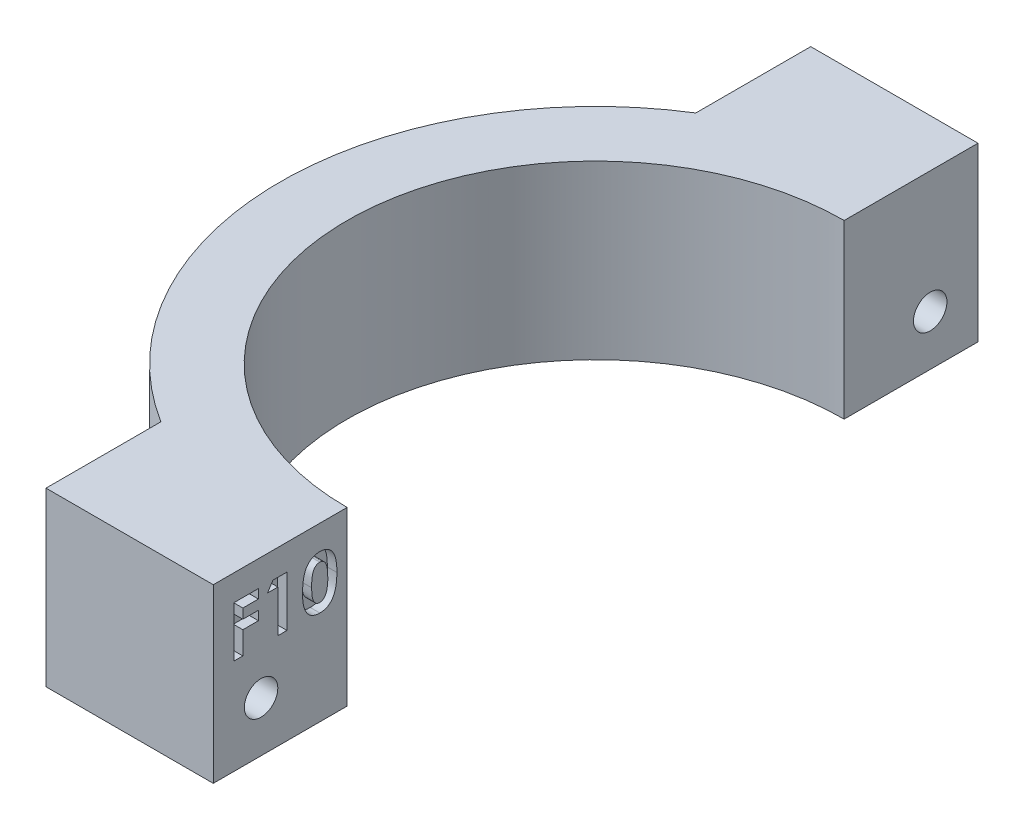
SolidWorks part; units mm, degrees
ref_plane "Front Plane" through (0, 0, 0) normal (0, 0, 1) x (1, 0, 0)
ref_plane "Top Plane" through (0, 0, 0) normal (0, 1, 0) x (1, 0, 0)
ref_plane "Right Plane" through (0, 0, 0) normal (1, 0, 0) x (0, 0, -1)
sketch "Sketch1" plane through (0, 0, 0) normal (0, 1, 0) x (1, 0, 0)
  line L0 (-46.9983, 32.5286) -> (-46.9983, -47.4714)
  line L1 (-46.9983, -47.4714) -> (-11.9983, -47.4714)
  line L2 (-11.9983, -47.4714) -> (-11.9983, -33.4714)
  line L3 (-46.9983, 32.5286) -> (-11.9983, 32.5286)
  line L4 (-11.9983, 32.5286) -> (-11.9983, 18.5286)
  line L5 (-29.4983, 32.5286) -> (-29.4983, 20.5062)
  line L6 (-29.4983, -47.4714) -> (-29.4983, -34.8576)
  arc A0 (-11.9983, 18.5286) -> (-11.9983, -33.4714) centre (-11.9983, -7.4714) ccw
  arc A1 (-11.9983, 25.5286) -> (-11.9983, -40.4714) centre (-11.9983, -7.4714) ccw
  dimension "D1" = 80
  dimension "D2" = 35
  dimension "D3" = 35
  dimension "D4" = 52
  dimension "D5" = 14
  dimension "D6" = 14
  dimension "D7" = 7
extrude "Boss-Extrude1" add sketch "Sketch1" along normal blind 18 contours A1 L4 L3 L5 | L4 A1 L2 A0 | A1 L6 L1 L2
sketch "Sketch2" plane through (-11.9983, 0, 0) normal (1, 0, 0) x (0, 0, -1)
  line L0 (-47.4714, 18) -> (-33.4714, 18) construction
  line L3 (32.5286, 18) -> (18.5286, 18) construction
  circle A0 centre (-42.4714, 5.25) radius 1.75
  circle A1 centre (27.5286, 5.25) radius 1.75
  dimension "D3" = 3.5
  dimension "D4" = 3.5
  dimension "D1" = 12.75
  dimension "D2" = 12.75
extrude "Cut-Extrude1" cut sketch "Sketch2" against normal through all
sketch "Sketch3" plane through (-11.9983, 0, 0) normal (1, 0, 0) x (0, 0, -1)
  text T0 "<b>F10</b>" font "Century Gothic" height in points 20
extrude "Cut-Extrude2" cut sketch "Sketch3" against normal blind 1
sketch "Sketch4" plane through (-29.4983, 0, 0) normal (-1, 0, 0) x (0, 0, 1)
  line L1 (-25.3918, 2.9011) -> (-24.4259, 5.926)
  line L2 (-24.4259, 5.926) -> (-26.5627, 8.275)
  line L3 (-26.5627, 8.275) -> (-29.6653, 7.5989)
  line L4 (-29.6653, 7.5989) -> (-30.6312, 4.574)
  line L5 (-30.6312, 4.574) -> (-28.4944, 2.225)
  line L6 (-28.4944, 2.225) -> (-25.3918, 2.9011)
  line L7 (44.7168, 3.0046) -> (45.5387, 6.0719)
  line L8 (45.5387, 6.0719) -> (43.2933, 8.3172)
  line L9 (43.2933, 8.3172) -> (40.2261, 7.4954)
  line L10 (40.2261, 7.4954) -> (39.4042, 4.4281)
  line L11 (39.4042, 4.4281) -> (41.6496, 2.1828)
  line L12 (41.6496, 2.1828) -> (44.7168, 3.0046)
  circle A0 centre (-27.5286, 5.25) radius 2.75 construction
  circle A1 centre (42.4714, 5.25) radius 2.75 construction
  dimension "D1" = 5.5
extrude "Cut-Extrude3" cut sketch "Sketch4" against normal blind 5
